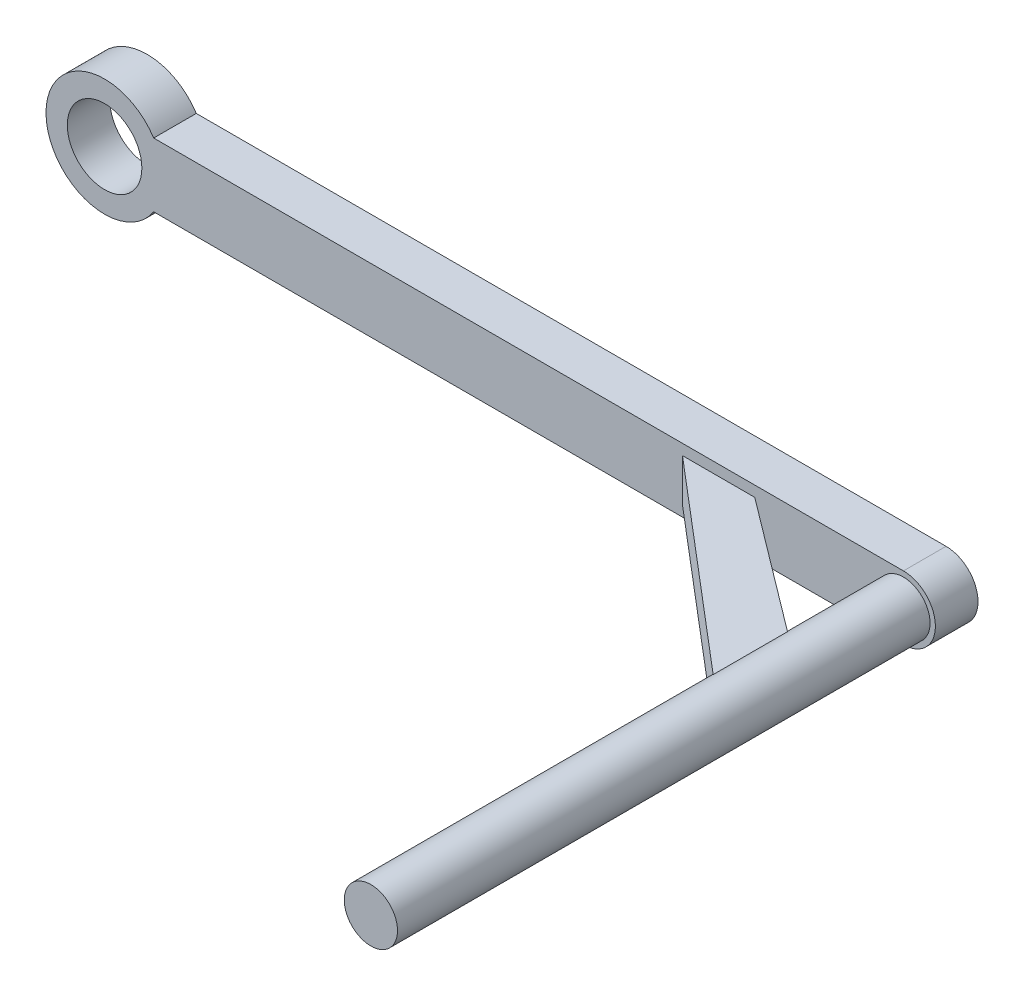
SolidWorks part; units mm, degrees
material "ABS"
ref_plane "Front Plane" through (0, 0, 0) normal (0, 0, 1) x (1, 0, 0)
ref_plane "Top Plane" through (0, 0, 0) normal (0, 1, 0) x (1, 0, 0)
ref_plane "Right Plane" through (0, 0, 0) normal (1, 0, 0) x (0, 0, -1)
sketch "Sketch1" plane through (0, 0, 0) normal (0, 0, 1) x (1, 0, 0)
  line L1 (0, -3) -> (-70.3902, -3)
  line L2 (0, 3) -> (-70.3902, 3)
  arc A0 (0, -3) -> (0, 3) centre (0, 0) ccw
  circle A2 centre (-75, 0) radius 3.5
  arc A3 (-70.3902, 3) -> (-70.3902, -3) centre (-75, 0) ccw
  point P3 (-37.5, 0)
  dimension "D1" = 7
  dimension "D2" = 3
  dimension "D4" = 11
extrude "Boss-Extrude1" add sketch "Sketch1" along normal blind 4
sketch "Sketch2" plane through (0, 0, 4) normal (0, 0, 1) x (1, 0, 0)
  circle A0 centre (0, 0) radius 2.5
  dimension "D1" = 5
extrude "Boss-Extrude2" add sketch "Sketch2" along normal blind 50
ref_plane "Plane1" through (0, 0, 0) normal (0, 1, 0) x (1, 0, 0)
sketch "Sketch3" plane through (0, 0, 0) normal (0, 1, 0) x (1, 0, 0)
  line L0 (-22.6269, -2.4001) -> (-16.0823, -2.4001)
  line L1 (-16.0823, -2.4001) -> (0, -14.5148)
  line L2 (0, -14.5148) -> (0, -21.639)
  line L3 (0, -21.639) -> (-22.6269, -2.4001)
extrude "Boss-Extrude3" add sketch "Sketch3" along normal blind 2 and the other way blind 2
